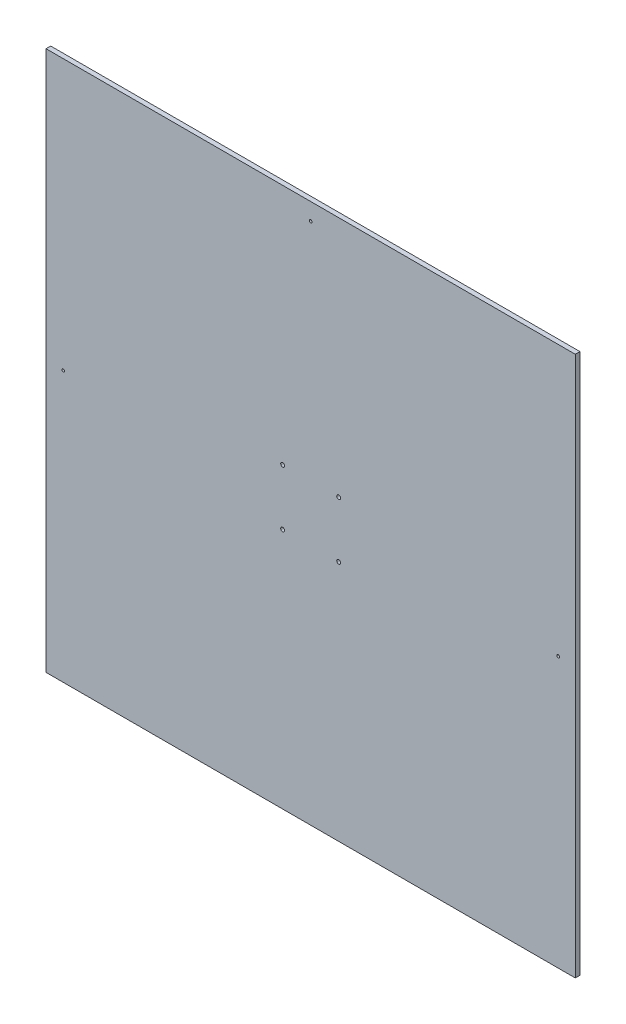
SolidWorks part; units mm, degrees
material "Pin"
ref_plane "Plan de face" through (0, 0, 0) normal (0, 0, 1) x (1, 0, 0)
ref_plane "Plan de dessus" through (0, 0, 0) normal (0, 1, 0) x (1, 0, 0)
ref_plane "Plan de droite" through (0, 0, 0) normal (1, 0, 0) x (0, 0, -1)
sketch "Esquisse1" plane through (0, 0, 0) normal (0, 0, 1) x (1, 0, 0)
  line L1 (340, 347) -> (-340, 347)
  line L2 (340, 347) -> (340, -347)
  line L3 (340, -347) -> (-340, -347)
  line L4 (-340, 347) -> (-340, -347)
  line L5 (340, 347) -> (-340, -347) construction
  line L6 (340, -347) -> (-340, 347) construction
  point P0 (0, 0)
  dimension "D1" = 680
  dimension "D2" = 694
extrude "Boss.-Extru.1" add sketch "Esquisse1" along normal blind 6
sketch "Esquisse2" plane through (0, 0, 6) normal (0, 0, 1) x (1, 0, 0)
  line L0 (0, -40) -> (0, 40) construction
  line L7 (-340, 0) -> (-318, 0) construction
  line L8 (-340, 347) -> (-340, -347) construction
  line L9 (340, 0) -> (318, 0) construction
  line L10 (0, 347) -> (0, 325) construction
  line L11 (340, 347) -> (-340, 347) construction
  circle A12 centre (-36, 36) radius 2.5
  circle A13 centre (-36, -36) radius 2.5
  circle A14 centre (36, -36) radius 2.5
  circle A15 centre (36, 36) radius 2.5
  circle A20 centre (-318, 0) radius 1.75
  circle A21 centre (318, 0) radius 1.75
  circle A22 centre (0, 325) radius 1.75
  point P21 (0, 0)
  dimension "D1" = 5
  dimension "D2" = 3.5
  dimension "D3" = 3.5
  dimension "D6" = 72
  dimension "D5" = 2
extrude "Enlèv. mat.-Extru.1" cut sketch "Esquisse2" against normal up to next
